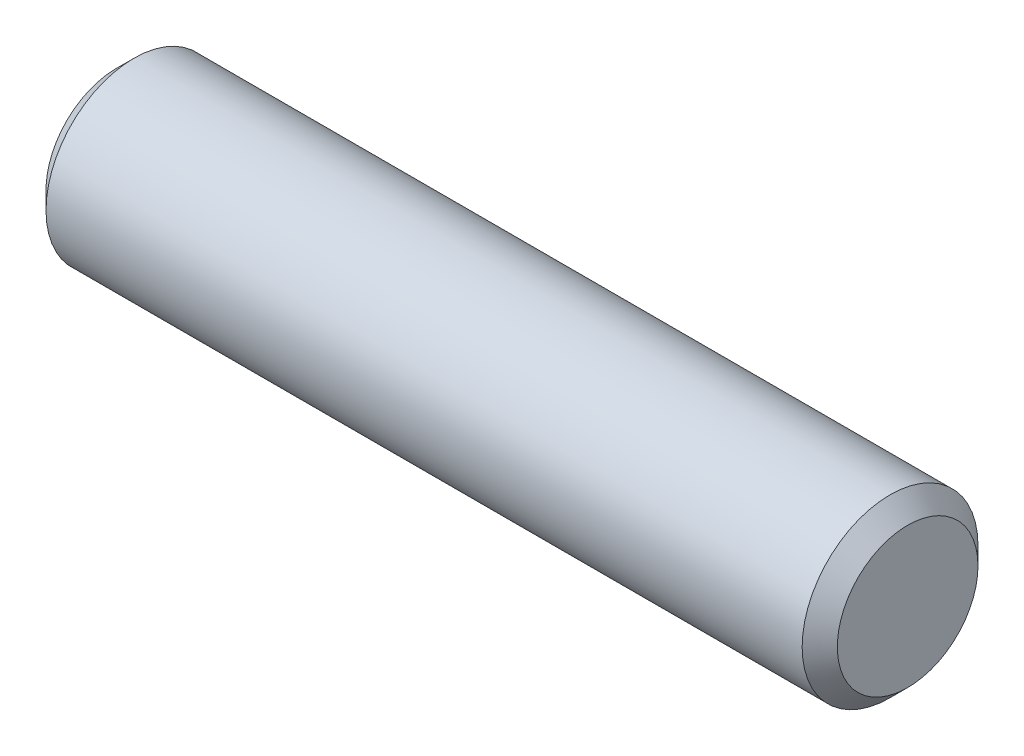
SolidWorks part; units mm, degrees
material "AISI 304"
ref_plane "Front" through (0, 0, 0) normal (0, 0, 1) x (1, 0, 0)
ref_plane "Top" through (0, 0, 0) normal (0, 1, 0) x (1, 0, 0)
ref_plane "Right" through (0, 0, 0) normal (1, 0, 0) x (0, 0, -1)
sketch "Sketch1" plane through (0, 0, 0) normal (0, 0, 1) x (1, 0, 0)
  line L0 (-28.575, 0) -> (28.575, 0) construction
  line L1 (28.575, 6.35) -> (28.575, -6.35) construction
  line L2 (-28.575, 6.35) -> (-28.575, -6.35) construction
  dimension "Length" = 57.15
  dimension "Diameter" = 12.7
sketch "Sketch2" plane through (0, 0, 0) normal (1, 0, 0) x (0, 0, -1)
  circle A0 centre (0, 0) radius 6.35
extrude "Extrude1" add sketch "Sketch2" against normal up to vertex (28.575 mm away) and the other way up to vertex (28.575 mm away) up to point (-28.575, 6.35, 0) other way up to point (28.575, 6.35, 0)
chamfer "Chamfer1" distance 1.27 angle 45 2 edges at (28.575, 0, -6.35) (-28.575, 0, -6.35)
equation "\"D1@Chamfer1\" = \"Diameter@Sketch1\"*.1"
